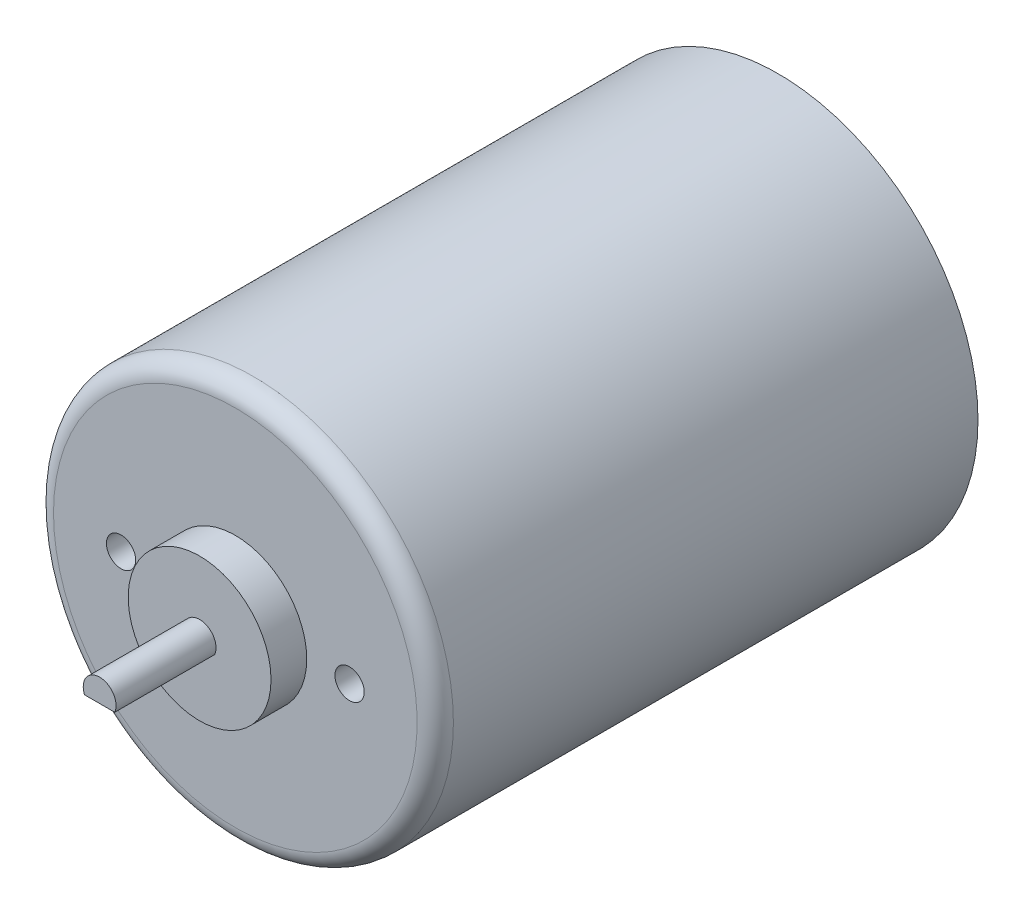
SolidWorks part; units mm, degrees
ref_plane "Front Plane" through (0, 0, 0) normal (0, 0, 1) x (1, 0, 0)
ref_plane "Top Plane" through (0, 0, 0) normal (0, 1, 0) x (1, 0, 0)
ref_plane "Right Plane" through (0, 0, 0) normal (1, 0, 0) x (0, 0, -1)
sketch "Sketch1" plane through (0, 0, 0) normal (1, 0, 0) x (0, 0, -1)
  line L0 (0, 0) -> (61.9063, 0) construction
  line L1 (-2.5, 0) -> (-2.5, 5)
  line L2 (-2.5, 5) -> (0, 5)
  line L3 (0, 5) -> (0, 14)
  line L4 (0, 14) -> (38, 14)
  line L5 (38, 14) -> (38, 0)
  line L6 (38, 0) -> (-2.5, 0)
  dimension "D1" = 28
  dimension "D2" = 10
  dimension "D3" = 38
  dimension "D4" = 2.5
revolve "Revolve1" add sketch "Sketch1" angle 360 about L0
sketch "Sketch2" plane through (0, 0, 2.5) normal (0, 0, 1) x (1, 0, 0)
  line L0 (-1.0583, -0.45) -> (1.0583, -0.45)
  arc A0 (1.0583, -0.45) -> (-1.0583, -0.45) centre (0, 0) ccw
  dimension "D1" = 1.15
  dimension "D2" = 1.6
extrude "Boss-Extrude1" add sketch "Sketch2" along normal blind 7
hole_wizard "M2.5x0.45 Tapped Hole1" positions "Sketch5" profile "Sketch6" tap size "M2.5x0.45" standard "ANSI Metric"
sketch "Sketch5" plane through (0, 0, 0) normal (0, 0, 1) x (1, 0, 0)
  line L0 (0, -5) -> (0, 5) construction
  circle A0 centre (0, 0) radius 5 construction
  circle A1 centre (0, 0) radius 5 construction
  point P0 (8, 0)
  point P2 (-8, 0)
  dimension "D1" = 16
cosmetic thread "Hole Thread1" parameters "D1"=5.08, "D2"=2.5
cosmetic thread "Hole Thread2" parameters "D1"=5.08, "D2"=2.5
sketch "Sketch6" plane through (8, 0, 0) normal (1, 0, 0) x (0, -1, 0)
  line L0 (0, 0) -> (0, 7.0421)
  line L1 (0, 7.0421) -> (1.025, 6.4262)
  line L2 (1.025, 6.4262) -> (1.025, 0)
  line L5 (1.025, 0) -> (0, 0)
  line L10 (0, 7.0421) -> (-1.025, 6.4262) construction
  line L11 (0, -6.35) -> (0, 107.95) construction
  dimension "Tap Drill Dia." = 2.05
  dimension "Tap Drill Depth" = 6.4262
  dimension "Drill Angle" = 118
fillet "Fillet1" radius 1.27 1 edges at (14, 0, 0)
